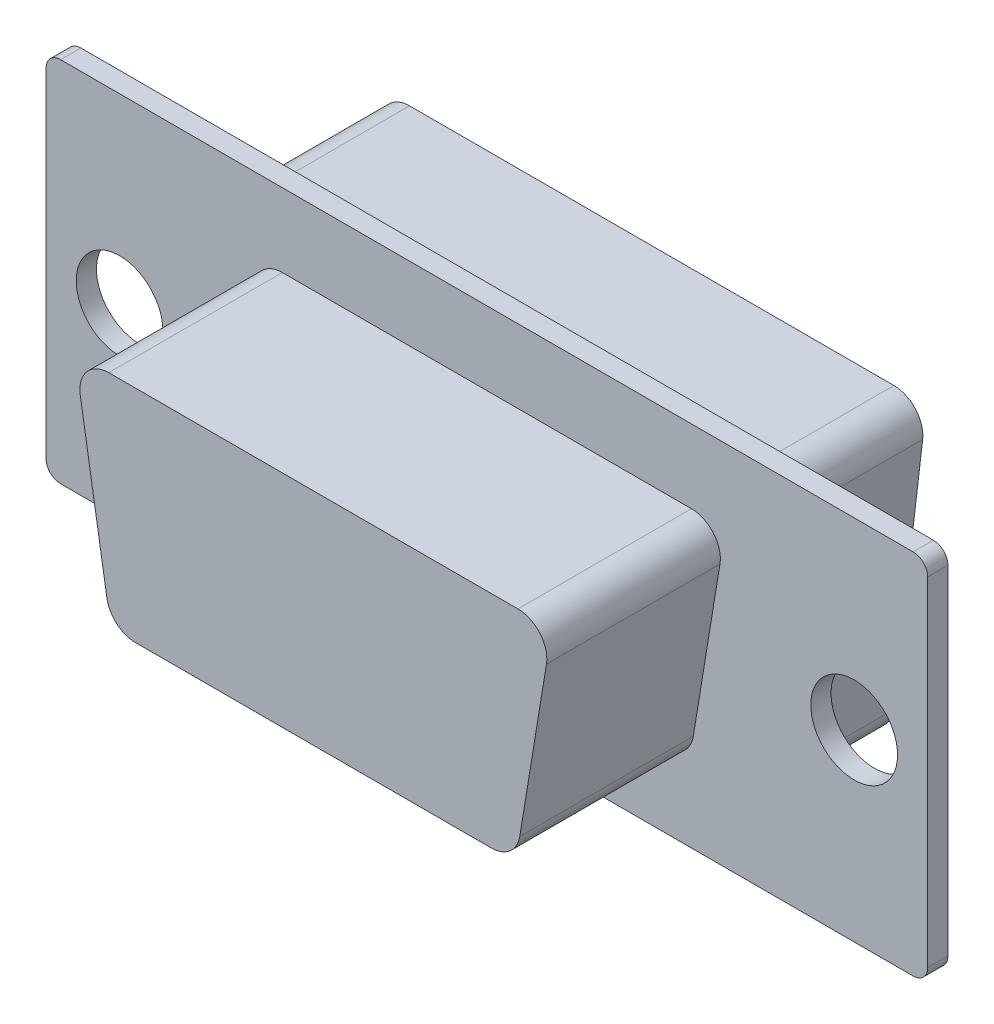
SolidWorks part; units mm, degrees
ref_plane "Front Plane" through (0, 0, 0) normal (0, 0, 1) x (1, 0, 0)
ref_plane "Top Plane" through (0, 0, 0) normal (0, 1, 0) x (1, 0, 0)
ref_plane "Right Plane" through (0, 0, 0) normal (1, 0, 0) x (0, 0, -1)
sketch "Esquisse1" plane through (0, 0, 0) normal (0, 0, 1) x (1, 0, 0)
  line L1 (-15.24, 6.35) -> (15.24, 6.35)
  line L2 (-15.24, 6.35) -> (-15.24, -6.35)
  line L3 (-15.24, -6.35) -> (15.24, -6.35)
  line L4 (15.24, 6.35) -> (15.24, -6.35)
  point P4 (0, 6.35)
  point P6 (-15.24, 0)
  dimension "D1" = 30.48
  dimension "D2" = 12.7
extrude "Boss.-Extru.1" add sketch "Esquisse1" along normal blind 0.7
fillet "Congé1" radius 0.5 4 edges at (-15.24, -6.35, 0.35) (15.24, -6.35, 0.35) (15.24, 6.35, 0.35) (-15.24, 6.35, 0.35)
sketch "Esquisse2" plane through (0, 0, 0.7) normal (0, 0, 1) x (1, 0, 0)
  circle A0 centre (-12.7, 0) radius 1.5
  circle A1 centre (12.7, 0) radius 1.5
  point P4 (0, 0)
  dimension "D1" = 3
  dimension "D2" = 25.4
  dimension "D3" = 12.7
extrude "Enlèv. mat.-Extru.1" cut sketch "Esquisse2" against normal through all
sketch "Esquisse3" plane through (0, 0, 0.7) normal (0, 0, 1) x (1, 0, 0)
  line L0 (-8.25, 3.81) -> (8.25, 3.81)
  line L1 (8.25, 3.81) -> (7, -3.81)
  line L2 (7, -3.81) -> (-7, -3.81)
  line L3 (-7, -3.81) -> (-8.25, 3.81)
  point P3 (0, 3.81)
  point P5 (-7.625, 0)
  point P7 (7, -2.8366)
  dimension "D1" = 16.5
  dimension "D2" = 14
  dimension "D3" = 7.62
extrude "Boss.-Extru.2" add sketch "Esquisse3" along normal blind 6
fillet "Congé2" radius 1 4 edges at (7, -3.81, 3.7) (8.25, 3.81, 3.7) (-7, -3.81, 3.7) (-8.25, 3.81, 3.7)
sketch "Esquisse4" plane through (0, 0, 0) normal (0, 0, -1) x (-1, 0, 0)
  line L0 (-9.5, 5.3) -> (9.5, 5.3)
  line L1 (9.5, 5.3) -> (8.25, -5.3)
  line L2 (8.25, -5.3) -> (-8.25, -5.3)
  line L3 (-8.25, -5.3) -> (-9.5, 5.3)
  line L4 (-15.24, -5.85) -> (-15.24, 5.85) construction
  line L5 (-14.74, 6.35) -> (14.74, 6.35) construction
  point P4 (-15.24, 0)
  point P7 (-8.875, 0)
  point P8 (0, 5.3)
  point P11 (0, 6.35)
  dimension "D1" = 10.6
  dimension "D2" = 19
  dimension "D3" = 16.5
extrude "Boss.-Extru.3" add sketch "Esquisse4" along normal blind 5
fillet "Congé3" radius 1 4 edges at (-8.25, -5.3, -2.5) (-9.5, 5.3, -2.5) (8.25, -5.3, -2.5) (9.5, 5.3, -2.5)
